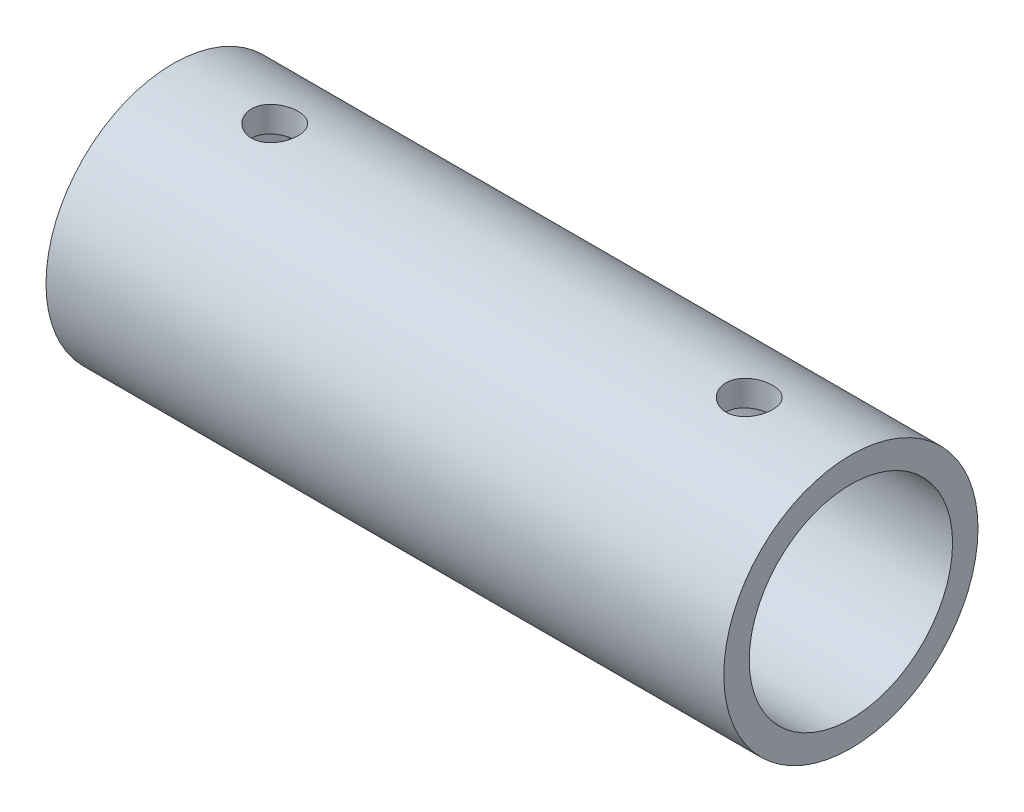
SolidWorks part; units mm, degrees
material "Alloy Steel"
ref_plane "Front Plane" through (0, 0, 0) normal (0, 0, 1) x (1, 0, 0)
ref_plane "Top Plane" through (0, 0, 0) normal (0, 1, 0) x (1, 0, 0)
ref_plane "Right Plane" through (0, 0, 0) normal (1, 0, 0) x (0, 0, -1)
sketch "Sketch1" plane through (0, 0, 0) normal (0, 0, 1) x (1, 0, 0)
  line L0 (-127, 0) -> (127, 0) construction
  line L1 (-127, 0) -> (-127, 47.625)
  line L2 (-127, 47.625) -> (127, 47.625)
  line L3 (127, 47.625) -> (127, 0) construction
  line L4 (-127, 0) -> (-120.65, 0)
  line L5 (-120.65, 0) -> (-120.65, 38.1)
  line L6 (-120.65, 38.1) -> (127, 38.1)
  line L7 (127, 47.625) -> (127, 38.1)
  dimension "D1" = 254
  dimension "D2" = 6.35
  dimension "D3" = 9.525
  dimension "D4" = 38.1
revolve "Revolve1" add sketch "Sketch1" angle 360 about L0
ref_plane "Plane1" through (0, 47.625, 0) normal (0, 1, 0) x (1, 0, 0)
sketch "Sketch2" plane through (0, 47.625, 0) normal (0, 1, 0) x (1, 0, 0)
  line L0 (88.9, 0) -> (-88.9, 0)
  point P4 (0, 0)
  point P6 (-88.9, 0)
  point P7 (88.9, 0)
  dimension "D1" = 177.8
hole_wizard "3/4-16 Tapped Hole1" positions "Sketch4" profile "Sketch3" tap size "3/4-16" standard "ANSI Inch"
sketch "Sketch4" plane through (0, 47.625, 0) normal (0, 1, 0) x (1, 0, 0)
  point P0 (-88.9, 0)
  point P3 (88.9, 0)
sketch "Sketch3" plane through (-88.9, 47.625, 0) normal (1, 0, 0) x (0, 0, 1)
  line L0 (0, 0) -> (0, 9.525)
  line L1 (0, 9.525) -> (8.7312, 9.525)
  line L2 (8.7312, 9.525) -> (8.7312, 0)
  line L5 (8.7312, 0) -> (0, 0)
  line L11 (0, -6.35) -> (0, 107.95) construction
  dimension "Thru Tap Drill Dia." = 17.4625
  dimension "Thru Tap Drill Depth" = 9.525
cosmetic thread "Hole Thread1"
cosmetic thread "Hole Thread2"
ref_plane "Plane2" through (0, 0, 47.625) normal (0, 0, 1) x (1, 0, 0)
sketch "Sketch5" plane through (0, 0, 47.625) normal (0, 0, 1) x (1, 0, 0)
  line L0 (0, 0) -> (-88.9, 0) construction
  point P4 (-88.9, 0)
  dimension "D1" = 88.9
